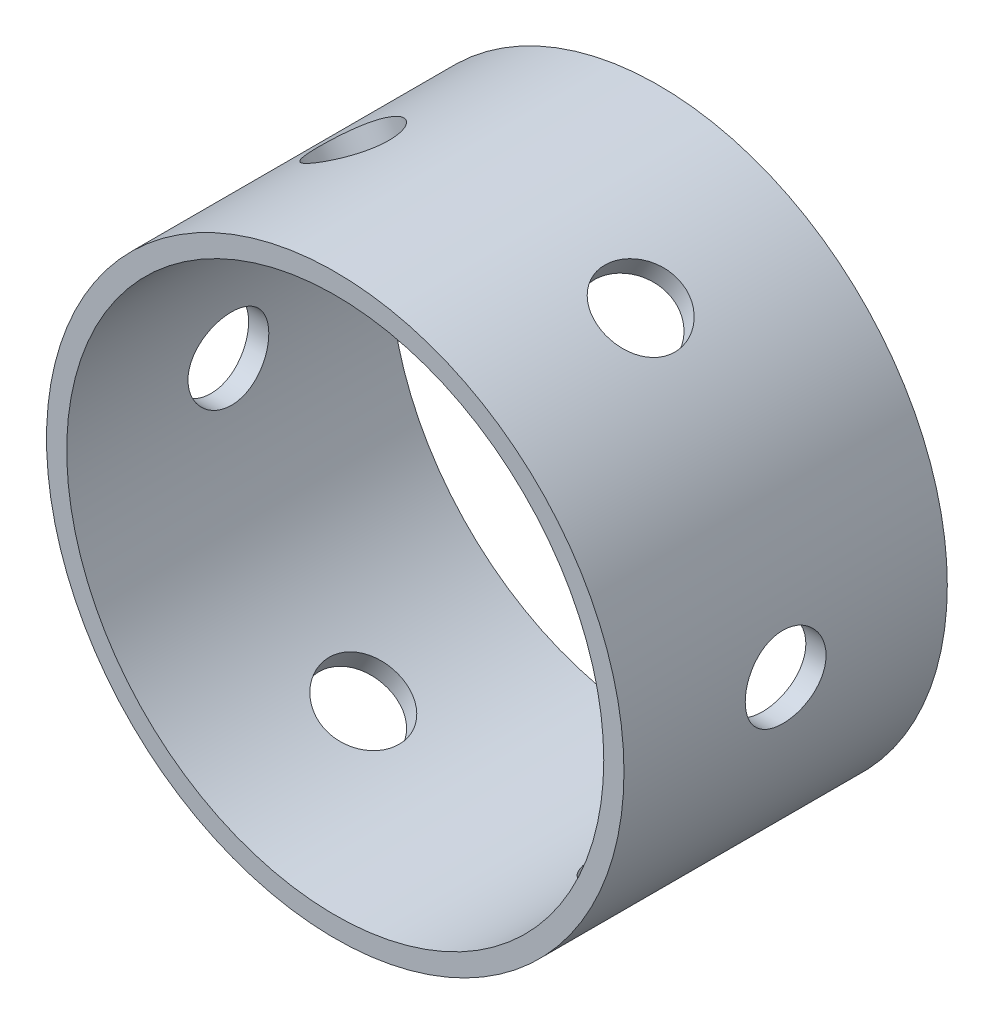
SolidWorks part; units mm, degrees
material "AISI 1020"
ref_plane "Plano frontal" through (0, 0, 0) normal (0, 0, 1) x (1, 0, 0)
ref_plane "Plano superior" through (0, 0, 0) normal (0, 1, 0) x (1, 0, 0)
ref_plane "Plano direito" through (0, 0, 0) normal (1, 0, 0) x (0, 0, -1)
sketch "Esboço1" plane through (0, 0, 0) normal (0, 0, 1) x (1, 0, 0)
  line L0 (0, 0) -> (-50000, 0) construction
  line L1 (0, -1000) -> (0, 49000) construction
  circle A0 centre (0, 0) radius 28.575
  circle A1 centre (0, 0) radius 26.575
  dimension "D2" = 57.15
  dimension "D1" = 2
extrude "Ressalto-extrusão1" add sketch "Esboço1" along normal blind 32 contours A0 | A1
sketch "Esboço2" plane through (0, 0, 0) normal (1, 0, 0) x (0, 0, -1)
  line L0 (-1000, 0) -> (49000, 0) construction
  circle A1 centre (-16, 0) radius 4
  point P1 (-16, 0)
  point P4 (-12, 0)
  dimension "D1" = 4
  dimension "D2" = 12
extrude "Corte-extrusão1" cut sketch "Esboço2" against normal blind 32
pattern_circular "PadrãoCircular1" count 6 over 360 about axis through (0, 0, 32) along (0, 0, -1) of "Corte-extrusão1"
equation "\"D2@Esboço1\"=25.4*(2.5-2*(1/8))"
equation "\"D1@Ressalto-extrusão1\"=4*8"
equation "\"D2@Esboço2\"=3*\"D1@Esboço2\""
